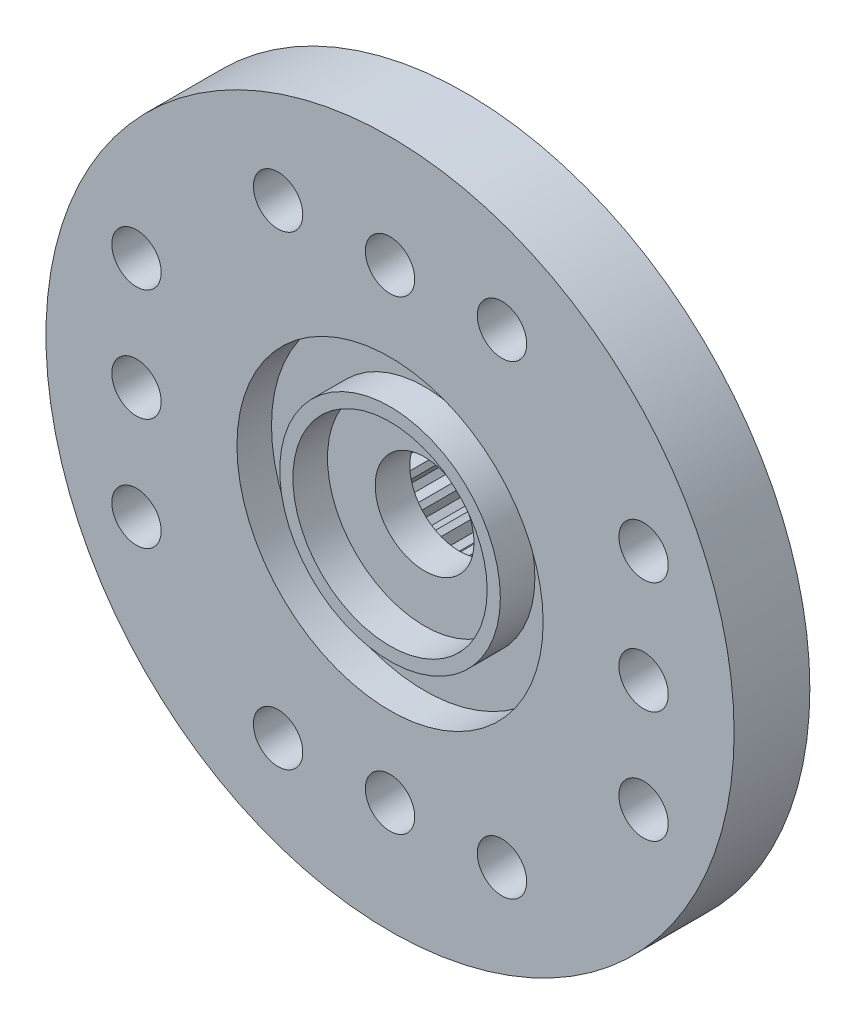
SolidWorks part; units mm, degrees
ref_plane "Ön Düzlem" through (0, 0, 0) normal (0, 0, 1) x (1, 0, 0)
ref_plane "Üst Düzlem" through (0, 0, 0) normal (0, 1, 0) x (1, 0, 0)
ref_plane "Sağ Düzlem" through (0, 0, 0) normal (1, 0, 0) x (0, 0, -1)
sketch "Çizim1" plane through (0, 0, 0) normal (0, 0, 1) x (1, 0, 0)
  circle A0 centre (0, 0) radius 4.45
  dimension "D1" = 8.9
extrude "Yükseklik-Ekstrüzyon1" add sketch "Çizim1" along normal blind 5.6
sketch "Çizim2" plane through (0, 0, 5.6) normal (0, 0, 1) x (1, 0, 0)
  line L0 (0, 0) -> (0, 4.45) construction
  line L1 (0, 0) -> (4.45, 0) construction
  circle A0 centre (0, 0) radius 10.45
  circle A1 centre (-7.7, 3.4) radius 0.75
  circle A2 centre (-7.7, 0) radius 0.75
  circle A3 centre (-7.7, -3.4) radius 0.75
  circle A4 centre (0, 7.07) radius 0.75
  circle A5 centre (3.4, 7.07) radius 0.75
  circle A6 centre (-3.4, 7.07) radius 0.75
  circle A7 centre (0, 0) radius 4.45 construction
  circle A8 centre (-3.4, -7.07) radius 0.75
  circle A9 centre (3.4, -7.07) radius 0.75
  circle A10 centre (0, -7.07) radius 0.75
  circle A11 centre (7.7, -3.4) radius 0.75
  circle A12 centre (7.7, 0) radius 0.75
  circle A13 centre (7.7, 3.4) radius 0.75
  point P8 (-7.7, 3.4)
  dimension "D1" = 3.4
  dimension "D3" = 3.4
  dimension "D2" = 3.4
  dimension "D4" = 3.4
extrude "Yükseklik-Ekstrüzyon2" add sketch "Çizim2" against normal blind 2.3
sketch "Çizim3" plane through (0, 0, 5.6) normal (0, 0, 1) x (1, 0, 0)
  circle A0 centre (0, 0) radius 2.95
  dimension "D1" = 5.9
extrude "Kes-Ekstrüzyon1" cut sketch "Çizim3" against normal blind 1.05
sketch "Çizim4" plane through (0, 0, 5.6) normal (0, 0, 1) x (1, 0, 0)
  circle A0 centre (0, 0) radius 3.35
  circle A1 centre (0, 0) radius 4.65
  dimension "D1" = 6.7
  dimension "D2" = 9.3
extrude "Kes-Ekstrüzyon2" cut sketch "Çizim4" against normal blind 1.05
sketch "Çizim5" plane through (0, 0, 4.55) normal (0, 0, 1) x (1, 0, 0)
  circle A0 centre (0, 0) radius 1.5
  dimension "D1" = 3
extrude "Kes-Ekstrüzyon3" cut sketch "Çizim5" against normal blind 11.05
sketch "Çizim6" plane through (0, 0, 0) normal (0, 0, -1) x (-1, 0, 0)
  circle A0 centre (0, 0) radius 2.68
  dimension "D1" = 5.36
extrude "Kes-Ekstrüzyon4" cut sketch "Çizim6" against normal blind 3.5
sketch "Çizim7" plane through (0, 0, 3.5) normal (0, 0, -1) x (-1, 0, 0)
  line L0 (-2.6011, 1.5927) -> (-2.4853, 1.7679)
  line L4 (-2.6011, 1.5927) -> (-2.3687, 1.2537)
  line L5 (-2.4853, 1.7679) -> (-2.0823, 1.6871)
  arc A0 (-2.0823, 1.6871) -> (-2.3687, 1.2537) centre (0, 0) ccw
  arc A1 (-2.4853, 1.7679) -> (-2.6011, 1.5927) centre (0, 0) ccw
  circle M4 centre (0, 0) radius 2.68
  dimension "D1" = 6.1
extrude "Kes-Ekstrüzyon5" cut sketch "Çizim7" along normal blind 3.5 contours L5 L0 L4 M4
pattern_circular "Dairesel Kaplama1" count 25 every 15 about axis through (0, 0, 0) along (0, 0, 1) of "Kes-Ekstrüzyon5"
